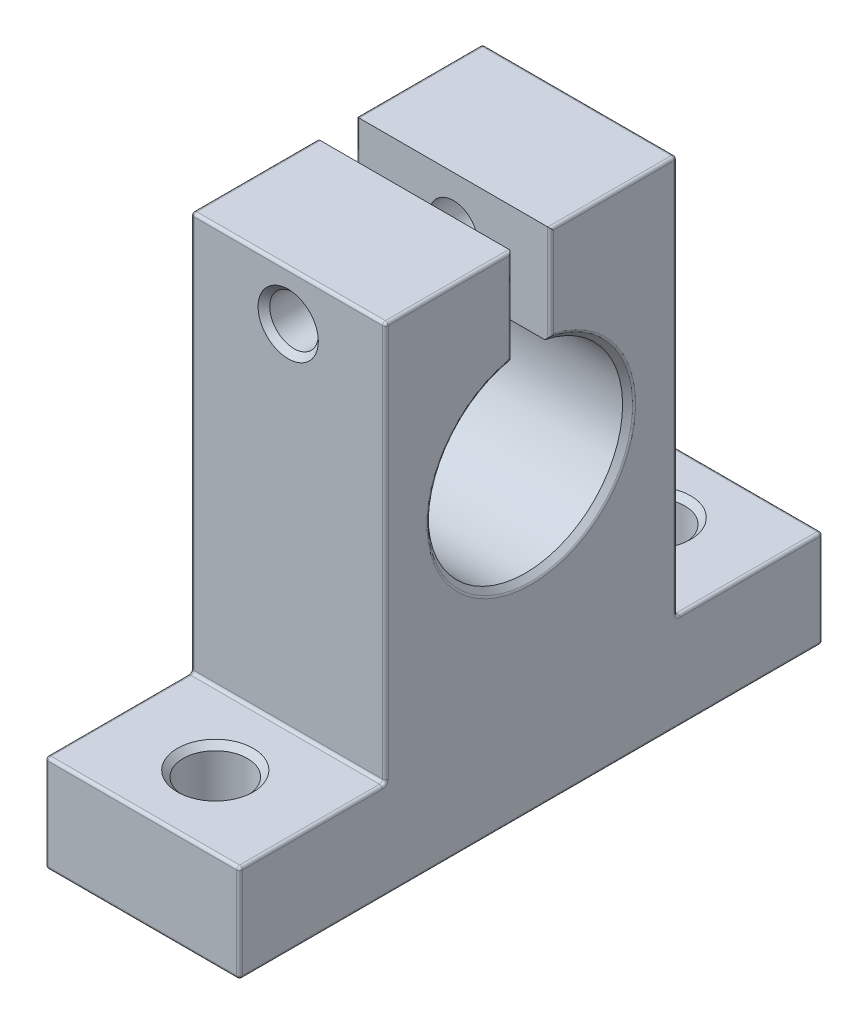
SolidWorks part; units mm, degrees
material "АМг 2 ГОСТ 4784-97"
ref_plane "Front Plane" through (0, 0, 0) normal (0, 0, 1) x (1, 0, 0)
ref_plane "Top Plane" through (0, 0, 0) normal (0, 1, 0) x (1, 0, 0)
ref_plane "Right Plane" through (0, 0, 0) normal (1, 0, 0) x (0, 0, -1)
sketch "Sketch1" plane through (0, 0, 0) normal (1, 0, 0) x (0, 0, -1)
  line L0 (-30, 0) -> (30, 0)
  line L1 (30, 0) -> (30, 10)
  line L2 (30, 10) -> (15, 10)
  line L3 (15, 10) -> (15, 51)
  line L4 (15, 51) -> (2, 51)
  line L5 (-15, 51) -> (-15, 10)
  line L6 (-15, 10) -> (-30, 10)
  line L7 (-30, 10) -> (-30, 0)
  line L8 (-2, 51) -> (-15, 51)
  line L9 (0, 0) -> (0, 64.8822) construction
  line L11 (-2, 40.798) -> (-2, 51)
  line L15 (2, 40.798) -> (2, 51)
  arc A0 (-2, 40.798) -> (2, 40.798) centre (0, 31) ccw
  dimension "D7" = 20
  dimension "D1" = 60
  dimension "D2" = 30
  dimension "D3" = 30
  dimension "D4" = 4
  dimension "D5" = 10
  dimension "D6" = 10
  dimension "D8" = 31
  dimension "D9" = 51
extrude "Boss-Extrude1" add sketch "Sketch1" along normal mid plane 20
sketch "Sketch2" plane through (0, 10, 0) normal (0, 1, 0) x (1, 0, 0)
  line L0 (23.1052, 0) -> (-16.2122, 0) construction
  circle A0 centre (0, -22.5) radius 3.3
  circle A1 centre (0, 22.5) radius 3.3
  dimension "D3" = 6.6
  dimension "D1" = 22.5
  dimension "D2" = 45
extrude "Cut-Extrude1" cut sketch "Sketch2" against normal through all
sketch "Sketch3" plane through (0, 0, -15) normal (0, 0, -1) x (-1, 0, 0)
  line L0 (-10, 51) -> (10, 51) construction
  circle A0 centre (0, 46) radius 2.5
  dimension "D1" = 5
  dimension "D2" = 5
extrude "Cut-Extrude2" cut sketch "Sketch3" against normal through all
sketch "Sketch4" plane through (0, 0, -15) normal (0, 0, -1) x (-1, 0, 0)
  circle A0 centre (0, 46) radius 4
  dimension "D1" = 8
extrude "Cut-Extrude3" cut sketch "Sketch4" against normal blind 5
chamfer "Фаска1" distance 0.6 angle 45 7 edges at (0, 0, -19.2) (0, 0, 25.8) (0, 48.5, 15) (-4, 46, -15) (0, 10, -19.2) (0, 10, 25.8) (10, 21, 0)
fillet "Скругление1" radius 0.3 32 edges at (-10, 0, 0) (-10, 5, -30) (-10, 10, -22.5) (-10, 30.5, -15) (-10, 51, -8.5) (-10, 45.899, -2) (-10, 21, 0) (-10, 45.899, 2) (-10, 51, 8.5) (-10, 30.5, 15) (-10, 10, 22.5) (-10, 5, 30) (10, 51, -8.5) (10, 30.5, -15) (10, 10, -22.5) (10, 5, -30) (10, 0, 0) (10, 5, 30) (10, 10, 22.5) (10, 30.5, 15) (10, 51, 8.5) (10, 46.2048, 2) (10, 20.4, 0) (10, 46.2048, -2) (0, 0, -30) (0, 10, -30) (0, 10, -15) (0, 51, -15) (0, 0, 30) (0, 10, 30) (0, 10, 15) (0, 51, 15)
